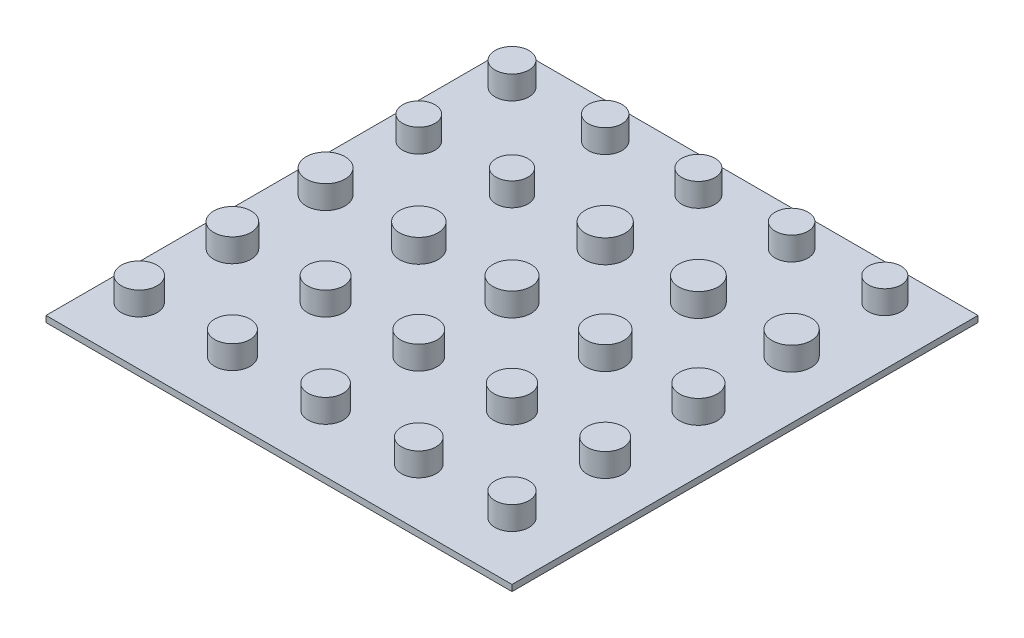
SolidWorks part; units mm, degrees
ref_plane "Front Plane" through (0, 0, 0) normal (0, 0, 1) x (1, 0, 0)
ref_plane "Top Plane" through (0, 0, 0) normal (0, 1, 0) x (1, 0, 0)
ref_plane "Right Plane" through (0, 0, 0) normal (1, 0, 0) x (0, 0, -1)
sketch "Sketch1" plane through (0, 0, 0) normal (0, 1, 0) x (1, 0, 0)
  line L1 (19.05, -19.05) -> (-19.05, -19.05)
  line L2 (19.05, -19.05) -> (19.05, 19.05)
  line L3 (19.05, 19.05) -> (-19.05, 19.05)
  line L4 (-19.05, -19.05) -> (-19.05, 19.05)
  line L5 (19.05, -19.05) -> (-19.05, 19.05) construction
  line L6 (19.05, 19.05) -> (-19.05, -19.05) construction
  point P0 (0, 0)
  dimension "D1" = 38.1
  dimension "D2" = 38.1
extrude "Boss-Extrude1" add sketch "Sketch1" along normal blind 0.508
sketch "Sketch2" plane through (0, 0.508, 0) normal (0, 1, 0) x (1, 0, 0)
  line L1 (0, 0) -> (-16.1633, 0) construction
  line L2 (0, 0) -> (0, 16.1633) construction
  line L3 (0, 16.1633) -> (-16.1633, 16.1633) construction
  line L4 (-16.1633, 0) -> (-16.1633, 16.1633) construction
  circle A0 centre (-16.1633, 16.1633) radius 1.3843
  circle A1 centre (-8.5433, 16.1633) radius 1.3716
  circle A2 centre (-0.9233, 16.1633) radius 1.3589
  circle A3 centre (6.6967, 16.1633) radius 1.3462
  circle A4 centre (14.3167, 16.1633) radius 1.3335
  circle A5 centre (-8.5433, 8.5433) radius 1.3081
  circle A6 centre (-0.9233, 8.5433) radius 1.6256
  circle A7 centre (6.6967, 8.5433) radius 1.6129
  circle A8 centre (14.3167, 8.5433) radius 1.6002
  circle A9 centre (-8.5433, 0.9233) radius 1.5748
  circle A10 centre (-0.9233, 0.9233) radius 1.5621
  circle A11 centre (6.6967, 0.9233) radius 1.5494
  circle A12 centre (14.3167, 0.9233) radius 1.5367
  circle A13 centre (-8.5433, -6.6967) radius 1.4732
  circle A14 centre (-0.9233, -6.6967) radius 1.4986
  circle A15 centre (6.6967, -6.6967) radius 1.4859
  circle A16 centre (14.3167, -6.6967) radius 1.4732
  circle A17 centre (-8.5433, -14.3167) radius 1.4478
  circle A18 centre (-0.9233, -14.3167) radius 1.4351
  circle A19 centre (6.6967, -14.3167) radius 1.4097
  circle A20 centre (14.3167, -14.3167) radius 1.397
  circle A21 centre (-16.1633, 8.5433) radius 1.3208
  circle A22 centre (-16.1633, 0.9233) radius 1.5875
  circle A23 centre (-16.1633, -6.6967) radius 1.524
  circle A24 centre (-16.1633, -14.3167) radius 1.4605
  dimension "D1" = 2.7686
  dimension "D4" = 2.6924
  dimension "D2" = 2.7432
  dimension "D3" = 2.7178
  dimension "D5" = 2.667
  dimension "D6" = 2.6416
  dimension ".103" = 2.6162
  dimension "D8" = 3.2512
  dimension "D9" = 3.2258
  dimension "D10" = 3.2004
  dimension "D11" = 3.175
  dimension "D12" = 3.1496
  dimension "D13" = 3.1242
  dimension "D14" = 3.0988
  dimension "D15" = 3.0734
  dimension "D16" = 3.048
  dimension "D17" = 2.9464
  dimension "D18" = 2.9972
  dimension "D19" = 2.9718
  dimension "D20" = 2.9464
  dimension "D21" = 2.921
  dimension "D22" = 2.8956
  dimension "D23" = 2.8702
  dimension "D24" = 2.8194
  dimension "D25" = 2.794
extrude "Boss-Extrude2" add sketch "Sketch2" along normal blind 1.905
